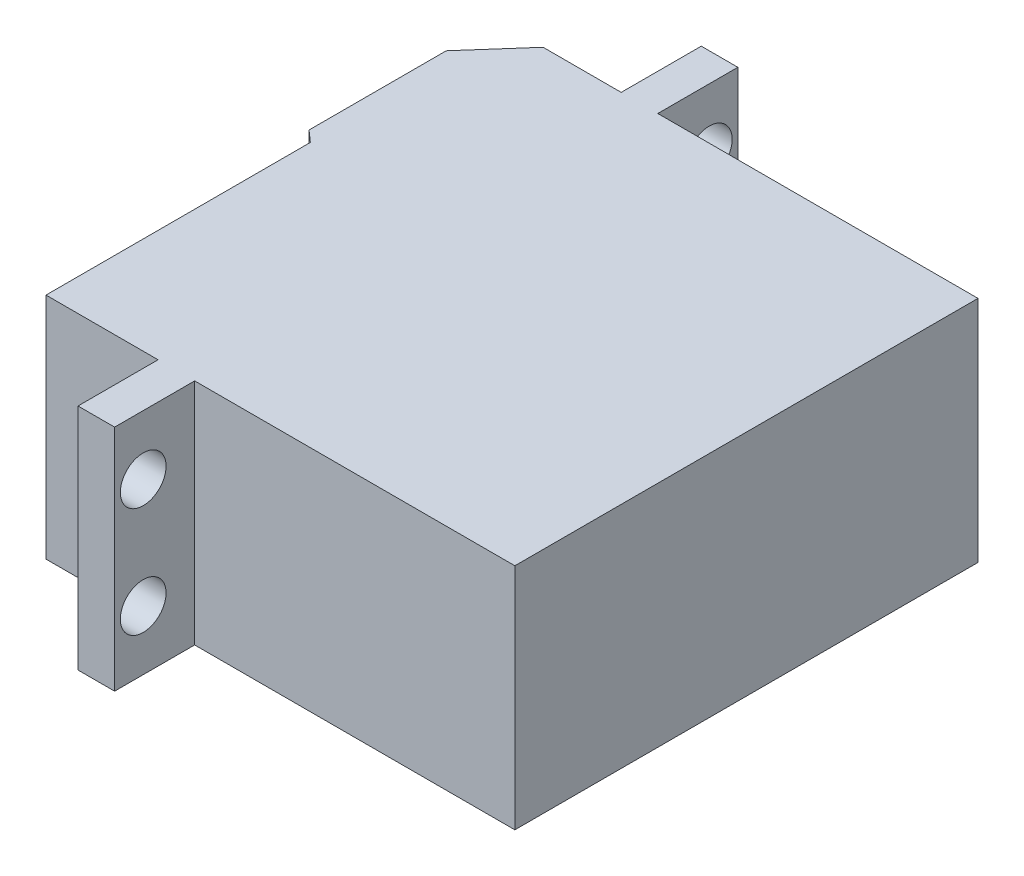
SolidWorks part; units mm, degrees
ref_plane "Front" through (0, 0, 0) normal (0, 0, 1) x (1, 0, 0)
ref_plane "Top" through (0, 0, 0) normal (0, 1, 0) x (1, 0, 0)
ref_plane "Right" through (0, 0, 0) normal (1, 0, 0) x (0, 0, -1)
sketch "Sketch1" plane through (0, 0, 0) normal (0, 1, 0) x (1, 0, 0)
  line L0 (0, 0) -> (0, 40.5)
  line L1 (0, 40.5) -> (-28, 40.5)
  line L2 (-28, 40.5) -> (-28, 47.5)
  line L3 (-28, 47.5) -> (-31.2, 47.5)
  line L4 (-31.2, 47.5) -> (-31.2, 40.5)
  line L5 (-31.2, 40.5) -> (-38.0314, 40.5)
  line L6 (-38.0314, 40.5) -> (-42, 36)
  line L7 (-42, 36) -> (-42, 24)
  line L8 (-42, 24) -> (-41, 23.1181)
  line L9 (-41, 23.1181) -> (-41, 0)
  line L10 (-41, 0) -> (-31.2, 0)
  line L11 (-31.2, 0) -> (-31.2, -7)
  line L12 (-31.2, -7) -> (-28, -7)
  line L13 (-28, -7) -> (-28, 0)
  line L14 (-28, 0) -> (0, 0)
  line L16 (-48, 33) -> (-42, 33) construction
  line L17 (-48, 33) -> (-48, 27) construction
  line L18 (-48, 27) -> (-42, 27) construction
  line L19 (-42, 33) -> (-42, 27) construction
  point P16 (-42, 30)
  point P17 (-48, 30)
  dimension "D1" = 41
  dimension "D2" = 40.5
  dimension "D3" = 7
  dimension "D4" = 28
  dimension "D5" = 3.2
  dimension "D6" = 1
  dimension "D7" = 12
  dimension "D8" = 6
  dimension "D9" = 27
  dimension "D10" = 6
extrude "Boss-Extrude1" add sketch "Sketch1" along normal blind 20
sketch "Sketch2" plane through (-42, 0, 0) normal (-1, 0, 0) x (0, 0, 1)
  line L0 (-30, 0) -> (-30, 20) construction
  line L1 (-33.4641, 10) -> (-31.7321, 7)
  line L2 (-31.7321, 7) -> (-28.2679, 7)
  line L3 (-28.2679, 7) -> (-26.5359, 10)
  line L4 (-26.5359, 10) -> (-28.2679, 13)
  line L5 (-28.2679, 13) -> (-31.7321, 13)
  line L6 (-31.7321, 13) -> (-33.4641, 10)
  line L7 (-36, 0) -> (-24, 0) construction
  line L8 (-36, 20) -> (-24, 20) construction
  line L9 (-36, 10) -> (-24, 10) construction
  line L10 (-36, 20) -> (-36, 0) construction
  line L11 (-24, 20) -> (-24, 0) construction
  circle A0 centre (-30, 10) radius 3 construction
  point P21 (-30, 10)
  dimension "D1" = 6
extrude "Boss-Extrude2" add sketch "Sketch2" along normal blind 4
sketch "Sketch3" plane through (-31.2, 0, 0) normal (-1, 0, 0) x (0, 0, 1)
  line L0 (-47.5, 10) -> (7, 10) construction
  line L1 (-47.5, 20) -> (-47.5, 0) construction
  line L2 (7, 20) -> (7, 0) construction
  line L3 (-20.25, 10) -> (-20.25, 20) construction
  line L4 (-23.1181, 20) -> (0, 20) construction
  line L6 (-40.5, 20) -> (-40.5, 0) construction
  circle A0 centre (-45, 5.2) radius 2
  circle A1 centre (-45, 14.8) radius 2
  circle A2 centre (4.5, 14.8) radius 2
  circle A3 centre (4.5, 5.2) radius 2
  dimension "D1" = 4
  dimension "D2" = 4.5
  dimension "D3" = 9.6
extrude "Cut-Extrude1" cut sketch "Sketch3" against normal through all
sketch "Sketch4" plane through (-46, 0, 0) normal (-1, 0, 0) x (0, 0, 1)
  line L0 (-26.5359, 10) -> (-33.4641, 10) construction
  circle A0 centre (-30, 10) radius 1.5
  point P7 (-30, 10)
  dimension "D1" = 3
extrude "Cut-Extrude2" cut sketch "Sketch4" against normal blind 2
equation "\"`27\"=27.8853"
equation "\"`0.1\"=2"
